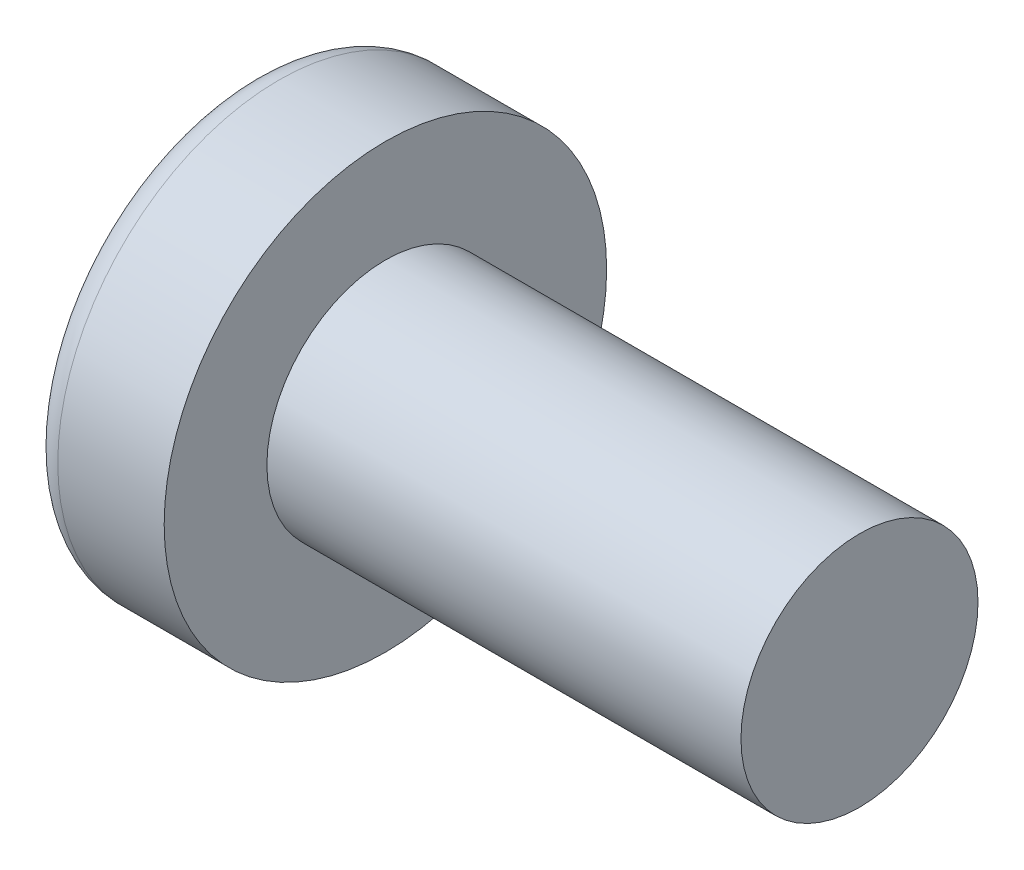
SolidWorks part; units mm, degrees
material "ABS"
ref_plane "Plane1" through (0, 0, 0) normal (0, 0, 1) x (1, 0, 0)
ref_plane "Plane2" through (0, 0, 0) normal (0, 1, 0) x (1, 0, 0)
ref_plane "Plane3" through (0, 0, 0) normal (1, 0, 0) x (0, 0, -1)
sketch "BodySke" plane through (0, 0, 0) normal (0, 0, 1) x (1, 0, 0)
  line L0 (2.4, 1.5) -> (2.4, 2.8)
  line L1 (2.9, 6.35) -> (2.9, -3.175) construction
  line L2 (-25.4, 0) -> (127, 0) construction
  line L3 (8.4, 0) -> (0, 0)
  line L4 (2.4, 1.5) -> (8.4, 1.5)
  line L5 (8.4, 1.5) -> (8.4, 0)
  line L6 (1.0534, 2.8) -> (2.4, 2.8)
  line L7 (2.4, -1.5) -> (8.4, -1.5) construction
  line L8 (2.4, 6.35) -> (2.4, -3.175) construction
  arc A0 (0.7472, 2.6293) -> (0, 0) centre (5, 0) ccw
  arc A2 (0.7472, 2.6293) -> (1.0534, 2.8) centre (1.0534, 2.44) cw
  dimension "Head_crown_rad" = 5
  dimension "Head_fillet_rad" = 0.36
  dimension "Diameter" = 3
  dimension "Length" = 6
  dimension "Head_ht" = 2.4
  dimension "Head_dia" = 5.6
  dimension "Advance" = 0.5
  dimension "Thread_nom" = 6
revolve "Base-Revolve" add sketch "BodySke" angle 360 about L2
cosmetic thread "ThreadCosmetic" [suppressed] parameters "Thread_length"=5.5, "Thread_minor"=2.439
sketch "Sketch3" plane through (0, 0, 0) normal (1, 0, 0) x (0, 0, -1)
  line L0 (0.37, -1.45) -> (-0.37, -1.45)
  line L1 (0.37, -1.45) -> (0.37, 1.45)
  line L2 (-0.37, 1.45) -> (0.37, 1.45)
  line L3 (-0.37, 1.45) -> (-0.37, -1.45)
  dimension "Cross_dia" = 2.9
  dimension "D1" = 1.45
  dimension "Cross_width" = 0.74
  dimension "D2" = 0.37
ref_plane "Plane4" through (1.76, 0, 0) normal (1, 0, 0) x (0, 0, -1)
sketch "Sketch4" plane through (1.76, 0, 0) normal (1, 0, 0) x (0, 0, -1)
  line L0 (0.185, -0.185) -> (-0.185, -0.185)
  line L1 (0.185, -0.185) -> (0.185, 0.185)
  line L2 (-0.185, 0.185) -> (0.185, 0.185)
  line L3 (-0.185, 0.185) -> (-0.185, -0.185)
  dimension "D2" = 0.37
  dimension "D1" = 0.37
  dimension "D3" = 0.185
  dimension "D4" = 0.185
loft "Cut-Loft1" cut profiles "Sketch3", "Sketch4"
pattern_circular "CirPattern1" count 2 every 90 about axis through (0, 0, 0) along (1, 0, 0) of "Cut-Loft1"
sketch "ThdSchSke" plane through (0, 0, 0) normal (0, 0, 1) x (1, 0, 0)
  line L0 (2.9, -1.2195) -> (2.7036, -1.5)
  line L1 (2.9, -1.2195) -> (3.0964, -1.5)
  line L2 (3.0964, -1.5) -> (3.0964, -1.875)
  line L3 (-3.175, 0) -> (5.1513, 0) construction
  line L5 (3.0964, -1.875) -> (2.7036, -1.875)
  line L6 (2.7036, -1.875) -> (2.7036, -1.5)
  dimension "Diameter" = 3
  dimension "SideAngle" = 55
  dimension "VeeAngle" = 70
  dimension "Thread_minor" = 2.439
  dimension "Overcut" = 3.75
  dimension "Start" = 2.9
revolve "ThreadSchematic" [suppressed] cut sketch "ThdSchSke" angle 360 about L3
pattern_linear "ThdSchPat" [suppressed]
equation "\"D1@Sketch3\" = \"Cross_dia@Sketch3\" / 2"
equation "\"D2@Sketch3\" = \"Cross_width@Sketch3\" / 2"
equation "\"D1@Sketch4\" = \"Cross_width@Sketch3\" *.5"
equation "\"D2@Sketch4\" = \"D1@Sketch4\""
equation "\"D3@Sketch4\" = \"D1@Sketch4\" / 2"
equation "\"D4@Sketch4\" = \"D2@Sketch4\" / 2"
equation "\"Thread_length@ThreadCosmetic\" = ((sgn( (\"Length@BodySke\" - \"Advance@BodySke\" ) - \"Thread_nom@BodySke\" )-1)*( (\"Length@BodySke\" - \"Advance@BodySke\" ) - \"Thread_nom@BodySke\" ))/-2+ \"Thread_nom@BodySke\""
equation "\"Thread_minor@ThdSchSke\" = \"Thread_minor@ThreadCosmetic\""
equation "\"Diameter@ThdSchSke\" = \"Diameter@BodySke\""
equation "\"Overcut@ThdSchSke\" = \"Diameter@BodySke\" * 1.25"
equation "\"Start@ThdSchSke\" = \"Head_ht@BodySke\" + \"Length@BodySke\" - \"Thread_length@ThreadCosmetic\"  '---Non-countersunk---"
equation "\"Num_threads@ThdSchPat\" = int( \"Thread_length@ThreadCosmetic\" / \"Advance@BodySke\" + 0.999 )  + 1"
equation "\"Advance@ThdSchPat\" = \"Thread_length@ThreadCosmetic\" /  (\"Num_threads@ThdSchPat\" - 1) 'relax it"
